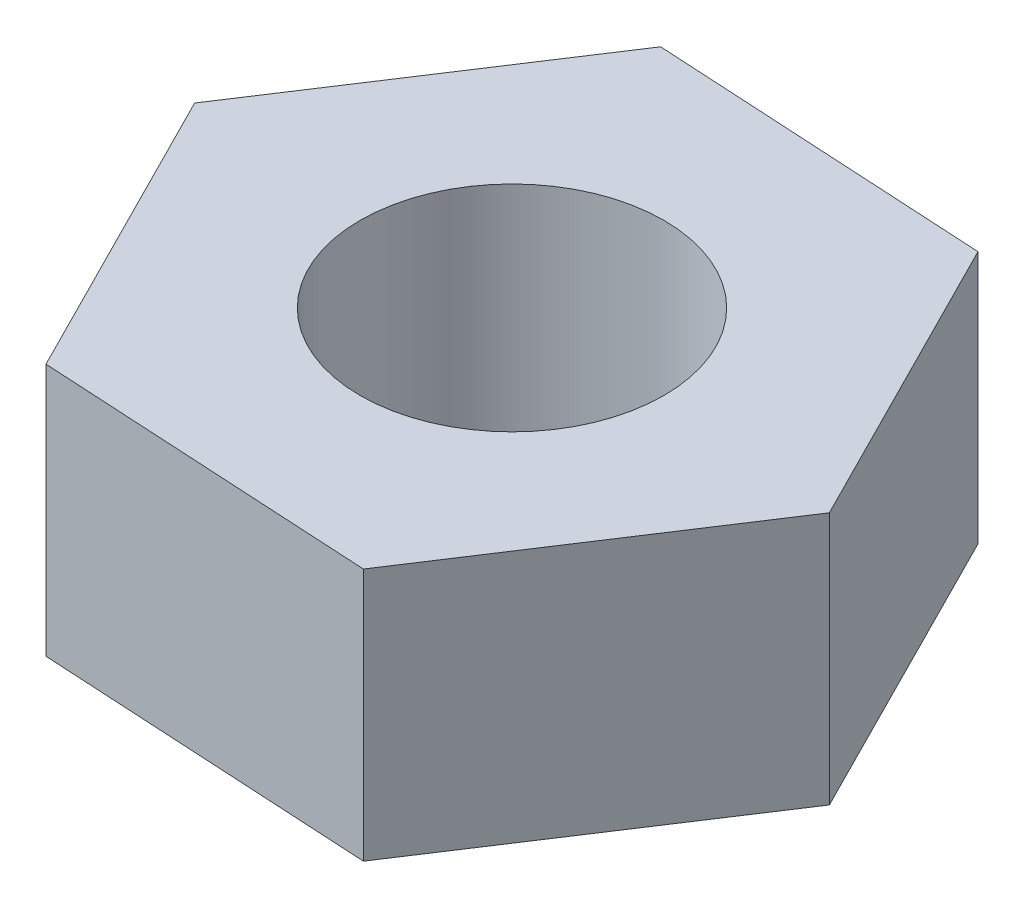
SolidWorks part; units mm, degrees
ref_plane "Front Plane" through (0, 0, 0) normal (0, 0, 1) x (1, 0, 0)
ref_plane "Top Plane" through (0, 0, 0) normal (0, 1, 0) x (1, 0, 0)
ref_plane "Right Plane" through (0, 0, 0) normal (1, 0, 0) x (0, 0, -1)
sketch "Sketch1" plane through (0, 0, 0) normal (0, 1, 0) x (1, 0, 0)
  line L1 (1.5, -2.9686) -> (3.3209, -0.1853)
  line L2 (3.3209, -0.1853) -> (1.8209, 2.7833)
  line L3 (1.8209, 2.7833) -> (-1.5, 2.9686)
  line L4 (-1.5, 2.9686) -> (-3.3209, 0.1853)
  line L5 (-3.3209, 0.1853) -> (-1.8209, -2.7833)
  line L6 (-1.8209, -2.7833) -> (1.5, -2.9686)
  circle A0 centre (0, 0) radius 32.5441
  circle A1 centre (0, 0) radius 1.5
  circle A2 centre (0, 0) radius 2.8804 construction
extrude "Boss-Extrude1" add sketch "Sketch1" along normal blind 2.5 contours L5 L6 L1 L2 L3 L4 A1
